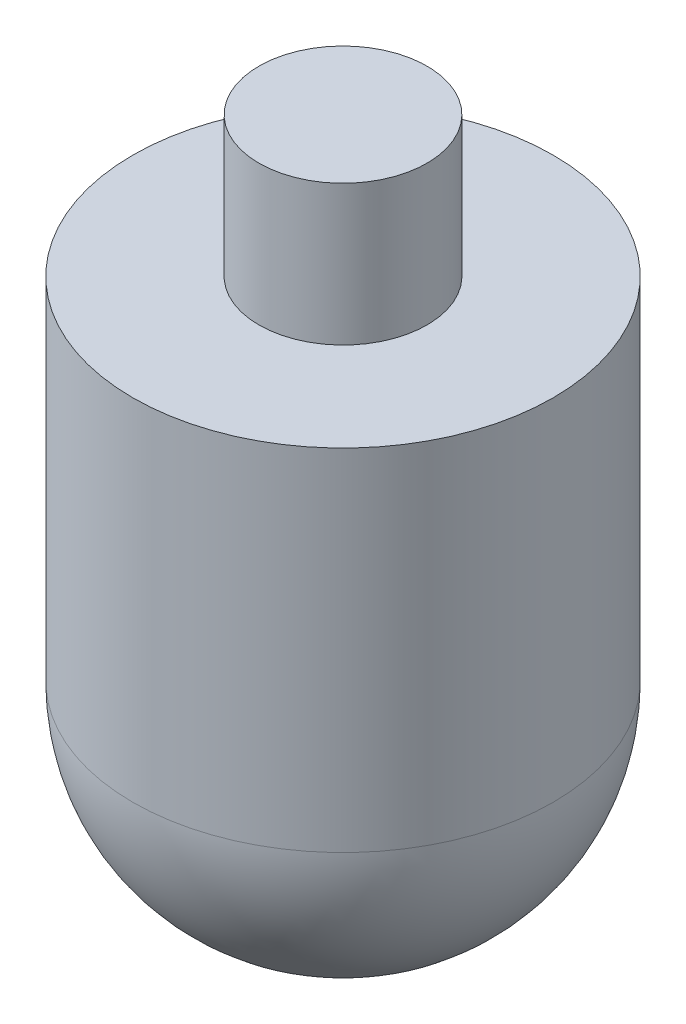
SolidWorks part; units mm, degrees
ref_plane "Front Plane" through (0, 0, 0) normal (0, 0, 1) x (1, 0, 0)
ref_plane "Top Plane" through (0, 0, 0) normal (0, 1, 0) x (1, 0, 0)
ref_plane "Right Plane" through (0, 0, 0) normal (1, 0, 0) x (0, 0, -1)
sketch "Sketch1" plane through (0, 0, 0) normal (0, 0, 1) x (1, 0, 0)
  line L1 (0, 0) -> (6, 0)
  line L2 (6, 0) -> (6, -10)
  line L3 (6, -10) -> (15, -10)
  line L4 (15, -10) -> (15, -35)
  line L5 (0, 10.75) -> (0, -62.5833) construction
  line L6 (0, 0) -> (0, -50)
  arc A0 (15, -35) -> (0, -50) centre (0, -35) cw
  dimension "D4" = 15
  dimension "D1" = 12
  dimension "D3" = 25
  dimension "D5" = 30
revolve "Revolve1" add sketch "Sketch1" angle 360 about L5
